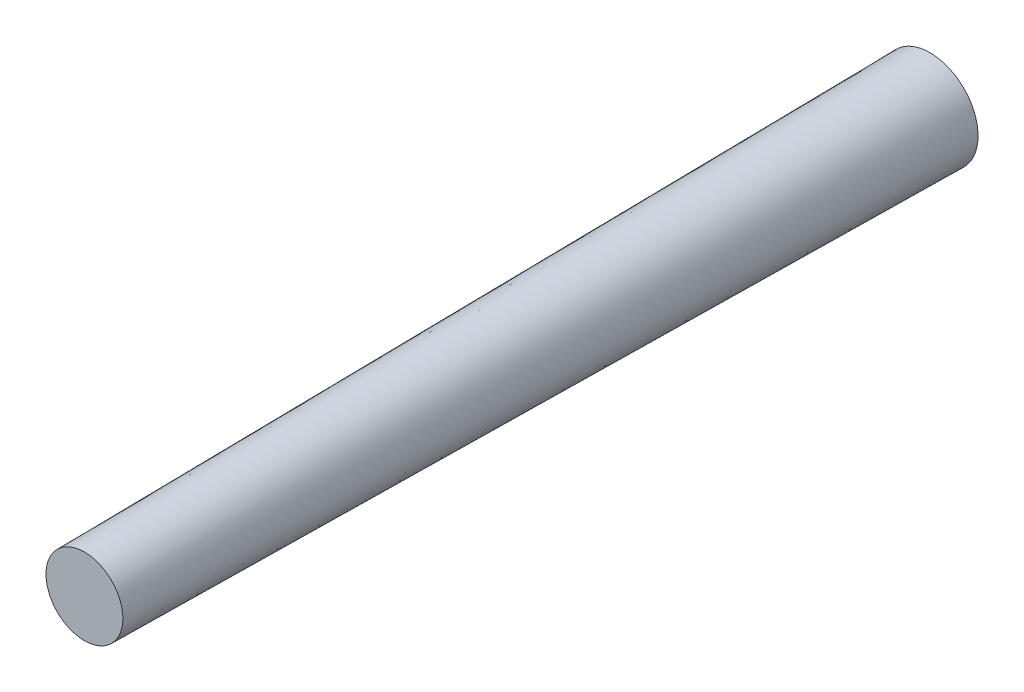
SolidWorks part; units mm, degrees
ref_plane "Front Plane" through (0, 0, 0) normal (0, 0, 1) x (1, 0, 0)
ref_plane "Top Plane" through (0, 0, 0) normal (0, 1, 0) x (1, 0, 0)
ref_plane "Right Plane" through (0, 0, 0) normal (1, 0, 0) x (0, 0, -1)
sketch "Sketch1" plane through (0, 0, 0) normal (0, 1, 0) x (1, 0, 0)
  line L0 (0, 92.7372) -> (0, -97.9449) construction
  line L1 (0, 22) -> (0, -22)
  line L2 (0, -22) -> (2, -22)
  line L3 (2, -22) -> (2.5, 22)
  line L4 (2.5, 22) -> (0, 22)
  dimension "D1" = 44
  dimension "D2" = 22
  dimension "D3" = 2
  dimension "D4" = 2.5
revolve "Revolve1" add sketch "Sketch1" angle 360 about L0
